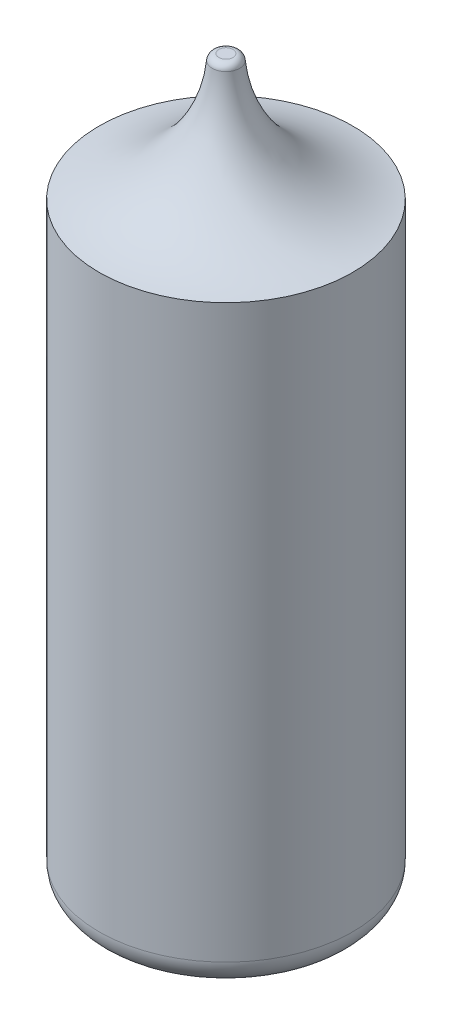
SolidWorks part; units mm, degrees
ref_plane "Front Plane" through (0, 0, 0) normal (0, 0, 1) x (1, 0, 0)
ref_plane "Top Plane" through (0, 0, 0) normal (0, 1, 0) x (1, 0, 0)
ref_plane "Right Plane" through (0, 0, 0) normal (1, 0, 0) x (0, 0, -1)
sketch "Sketch2" plane through (0, 0, 0) normal (1, 0, 0) x (0, 0, -1)
  line L0 (0, 0) -> (7.55, 0)
  line L1 (9.55, 2) -> (9.55, 45)
  line L2 (0, 54.5) -> (0, 0)
  line L3 (0, 54.5) -> (0.5304, 54.5)
  arc A1 (7.55, 0) -> (9.55, 2) centre (7.55, 2) ccw
  arc A2 (9.55, 45) -> (1.0286, 54.0426) centre (10.9922, 54.8955) cw
  arc A3 (0.5304, 54.5) -> (1.0286, 54.0426) centre (0.5304, 54) cw
  point P9 (9.55, 0)
  point P11 (1.4297, 54.3366)
  point P13 (1, 54.5)
  dimension "D4" = 1
  dimension "D5" = 2
  dimension "D6" = 10
  dimension "D7" = 0.5
  dimension "D1" = 54.5
  dimension "D2" = 9.55
  dimension "D3" = 45
revolve "Revolve1" add sketch "Sketch2" angle 360 about L2
